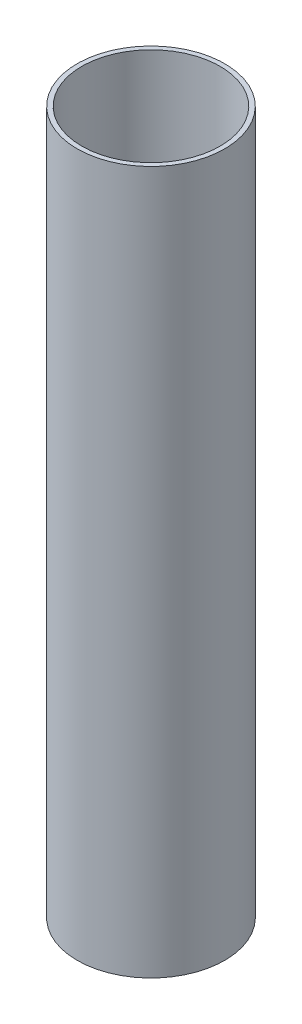
SolidWorks part; units mm, degrees
material "Silicon Dioxide"
ref_plane "Front Plane" through (0, 0, 0) normal (0, 0, 1) x (1, 0, 0)
ref_plane "Top Plane" through (0, 0, 0) normal (0, 1, 0) x (1, 0, 0)
ref_plane "Right Plane" through (0, 0, 0) normal (1, 0, 0) x (0, 0, -1)
sketch "Sketch1" plane through (0, 0, 0) normal (0, 1, 0) x (1, 0, 0)
  circle A0 centre (0, 0) radius 37.5
  circle A1 centre (0, 0) radius 40
  dimension "D1" = 80
  dimension "D2" = 75
extrude "Boss-Extrude1" add sketch "Sketch1" along normal blind 381
